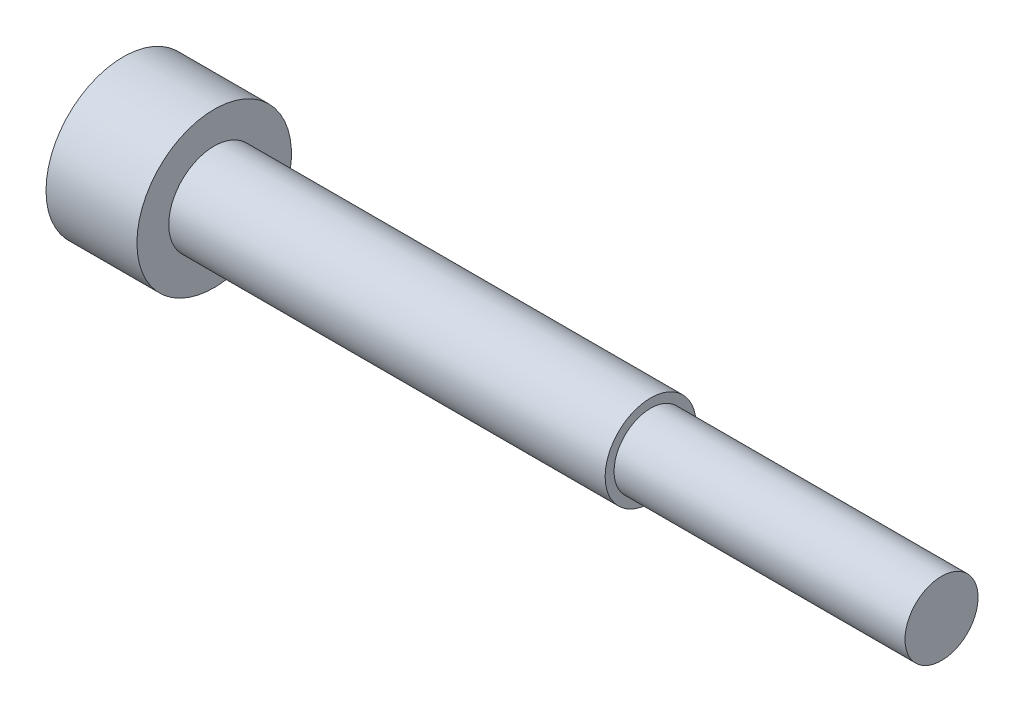
SolidWorks part; units mm, degrees
ref_plane "Vorne" through (0, 0, 0) normal (0, 0, 1) x (1, 0, 0)
ref_plane "Oben" through (0, 0, 0) normal (0, 1, 0) x (1, 0, 0)
ref_plane "Rechts" through (0, 0, 0) normal (1, 0, 0) x (0, 0, -1)
sketch "Skizze1" plane through (0, 0, 0) normal (0, 0, 1) x (1, 0, 0)
  line L0 (0, 0) -> (37.6304, 0) construction
  line L1 (40, 0) -> (40, 2.0095)
  line L3 (40, 2.0095) -> (0, 2.0095)
  line L4 (0, 2.0095) -> (0, 4.25)
  line L5 (0, 4.25) -> (-5, 4.25)
  line L6 (-5, 4.25) -> (-5, 0)
  line L7 (-5, 0) -> (40, 0)
  dimension "Dk" = 4.019
  dimension "D2" = 8.5
  dimension "k" = 5
  dimension "l" = 40
revolve "Basis-Rotation" add sketch "Skizze1" angle 360 about L0
sketch "Skizze2" plane through (-5, 0, 0) normal (-1, 0, 0) x (0, 0, 1)
  line L1 (2.3094, 0) -> (1.1547, 2)
  line L2 (1.1547, 2) -> (-1.1547, 2)
  line L3 (-1.1547, 2) -> (-2.3094, 0)
  line L4 (-2.3094, 0) -> (-1.1547, -2)
  line L5 (-1.1547, -2) -> (1.1547, -2)
  line L6 (1.1547, -2) -> (2.3094, 0)
  circle A0 centre (0, 0) radius 2 construction
  dimension "sw" = 4
extrude "Schnitt-Linear austragen1" cut sketch "Skizze2" against normal blind 3.65
sketch "Skizze3" plane through (0, 0, 0) normal (1, 0, 0) x (0, 0, -1)
  circle A0 centre (0, 0) radius 2.5
  dimension "dn" = 5
extrude "Aufsatz-Linear austragen1" add sketch "Skizze3" along normal offset from surface (24 mm away) 16 up to face at (40, 0, 2.0095)
